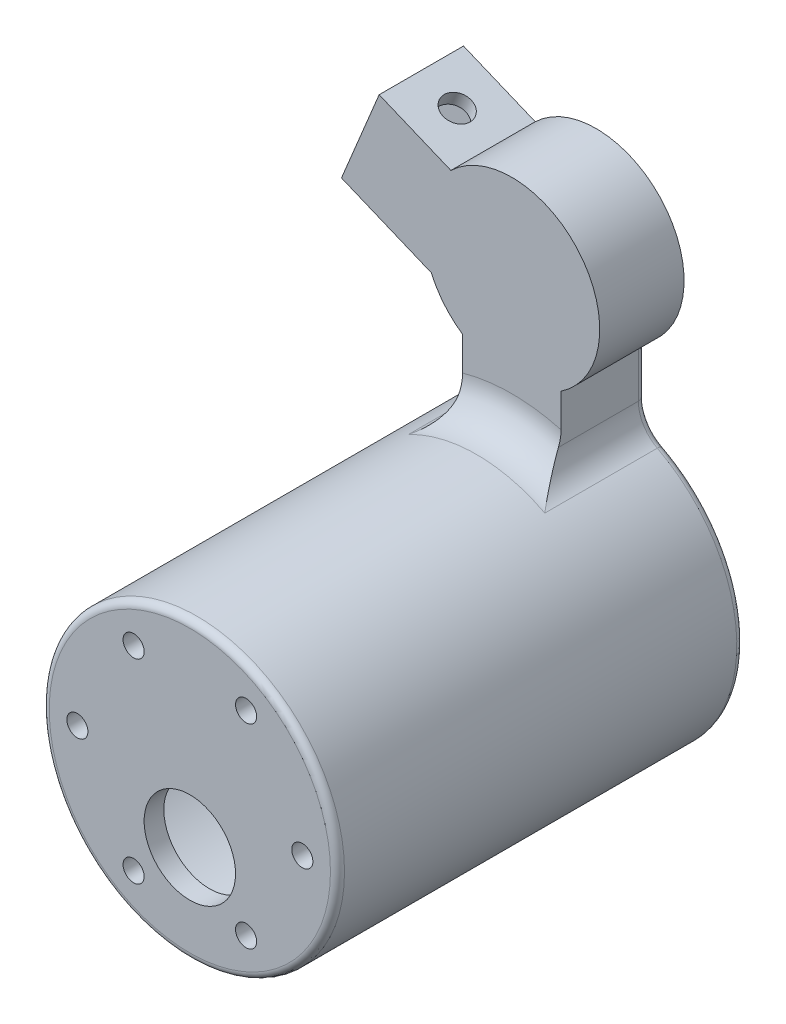
SolidWorks part; units mm, degrees
ref_plane "Front Plane" through (0, 0, 0) normal (0, 0, 1) x (1, 0, 0)
ref_plane "Top Plane" through (0, 0, 0) normal (0, 1, 0) x (1, 0, 0)
ref_plane "Right Plane" through (0, 0, 0) normal (1, 0, 0) x (0, 0, -1)
sketch "Sketch1" plane through (0, 0, 0) normal (0, 0, 1) x (1, 0, 0)
  line L0 (0, 0) -> (-12.5, 0) construction
  line L1 (0, 0) -> (-11.5485, -4.7835) construction
  line L2 (24.2314, 0.2955) -> (11.4585, -4.9953)
  line L3 (0, 0) -> (0, 10) construction
  line L4 (20.7873, 8.6104) -> (24.2314, 0.2955)
  line L5 (20.7873, 8.6104) -> (18.8739, 13.2298)
  line L6 (18.8739, 13.2298) -> (8.671, 9.0036)
  line L8 (0, 0) -> (0, -15.9469) construction
  line L9 (0, -15.9469) -> (-7, -15.9469) construction
  line L12 (-20.7873, -8.6104) -> (-11.5485, -4.7835) construction
  line L15 (0, -15.9469) -> (7, -15.9469) construction
  line L16 (-20.7873, 8.6104) -> (-18.8739, 13.2298)
  line L17 (7, -10.3562) -> (7, -20.3562)
  line L18 (7, -20.3562) -> (-7, -20.3562)
  line L19 (-7, -20.3562) -> (-7, -10.3562)
  line L20 (-18.8739, 13.2298) -> (-8.671, 9.0036)
  line L21 (-20.7873, 8.6104) -> (-24.2314, 0.2955)
  line L22 (-24.2314, 0.2955) -> (-11.4585, -4.9953)
  circle A3 centre (0, 0) radius 12.5
  circle A4 centre (0, 0) radius 10
  dimension "D1" = 25
  dimension "D3" = 22.5
  dimension "D2" = 20
  dimension "D4" = 10
  dimension "D5" = 14
  dimension "D6" = 10
extrude "Boss-Extrude2" add sketch "Sketch1" along normal blind 12 contours A3
sketch "Sketch2" plane through (0, 0, 0) normal (0, 0, 1) x (1, 0, 0)
  line L8 (7, -10.3562) -> (7, -20.3562) construction
  line L9 (7, -20.3562) -> (-7, -20.3562) construction
  line L10 (-7, -20.3562) -> (-7, -10.3562) construction
  line L11 (7, -10.3562) -> (7, -20.3562)
  line L12 (7, -20.3562) -> (-7, -20.3562)
  line L13 (-7, -20.3562) -> (-7, -10.3562)
  line L14 (-24.2314, 0.2955) -> (-11.4585, -4.9953) construction
  line L15 (-20.7873, 8.6104) -> (-24.2314, 0.2955) construction
  line L16 (-20.7873, 8.6104) -> (-18.8739, 13.2298) construction
  line L17 (-18.8739, 13.2298) -> (-8.671, 9.0036) construction
  line L18 (-24.2314, 0.2955) -> (-11.4585, -4.9953)
  line L19 (-20.7873, 8.6104) -> (-24.2314, 0.2955)
  line L20 (-20.7873, 8.6104) -> (-18.8739, 13.2298)
  line L21 (-18.8739, 13.2298) -> (-8.671, 9.0036)
  circle A0 centre (0, 0) radius 12.5 construction
  arc A4 (-8.671, 9.0036) -> (-11.4585, -4.9953) centre (0, 0) ccw
  arc A5 (-7, -10.3562) -> (7, -10.3562) centre (0, 0) ccw
extrude "Boss-Extrude3" add sketch "Sketch2" along normal blind 12
sketch "Sketch5" plane through (0, 0, 0) normal (0, 0, 1) x (1, 0, 0)
  line L0 (0, -20.3562) -> (0, -40.1562) construction
  line L2 (-7, -20.3562) -> (7, -20.3562) construction
  circle A1 centre (0, -40.1562) radius 21.001
  dimension "D1" = 19.8
extrude "Boss-Extrude4" add sketch "Sketch5" along normal blind 57.8
sketch "Sketch6" plane through (0, 0, 0) normal (0, 0, -1) x (-1, 0, 0)
  line L0 (-21.001, -40.1562) -> (0, -40.1562) construction
  arc A2 (-7, -20.3562) -> (7, -20.3562) centre (0, -40.1562) ccw construction
  circle A3 centre (0, -40.1562) radius 19
extrude "Cut-Extrude3" cut sketch "Sketch6" against normal blind 55
sketch "Sketch7" plane through (0, 0, 57.8) normal (0, 0, 1) x (1, 0, 0)
  line L0 (-21.001, -40.1562) -> (21.001, -40.1562) construction
  line L1 (0, -40.1562) -> (0, -47.1562) construction
  line L2 (-19, -40.1562) -> (-16, -40.1562) construction
  circle A2 centre (0, -47.1562) radius 6.5
  circle A3 centre (-16, -40.1562) radius 1.5
  circle A5 centre (-8, -54.0126) radius 1.5
  circle A6 centre (8, -54.0126) radius 1.5
  circle A7 centre (16, -40.1562) radius 1.5
  circle A8 centre (8, -26.2998) radius 1.5
  circle A9 centre (-8, -26.2998) radius 1.5
  point P28 (0, -40.1562)
  dimension "D1" = 7
  dimension "D2" = 6
extrude "Cut-Extrude4" cut sketch "Sketch7" against normal through all
fillet "Fillet1" radius 5 3 edges at (7, -20.3562, 6) (-7, -20.3562, 6) (0, -19.1552, 12)
fillet "Fillet2" radius 1 7 edges at (-7, -13.7231, 0) (7, -13.7231, 0) (-7.7258, -19.6844, 0) (7.7258, -19.6844, 0) (0, -61.1571, 0) (-19, -40.1562, 0) (21.001, -40.1562, 57.8)
sketch "Sketch8" plane through (-20.7873, 8.6104, 0) normal (-0.9239, 0.3827, 0) x (0, 0, 1)
  line L0 (12, 5) -> (0, 5) construction
  line L1 (2, 3) -> (10, 3)
  line L2 (2, 3) -> (2, -7)
  line L3 (2, -7) -> (10, -7)
  line L4 (10, 3) -> (10, -7)
  line L5 (12, -9) -> (0, -9) construction
  line L6 (0, 5) -> (0, -9) construction
  line L7 (12, 5) -> (12, -9) construction
  dimension "D1" = 2
  dimension "D2" = 2
  dimension "D3" = 2
  dimension "D4" = 2
extrude "Cut-Extrude5" cut sketch "Sketch8" against normal blind 10
sketch "Sketch9" plane through (1.9134, 4.6194, 0) normal (0.3827, 0.9239, 0) x (0.9239, -0.3827, 0)
  line L0 (-16.9782, 0) -> (-16.9782, -12) construction
  line L5 (-22.5, -6) -> (-11.4564, -6) construction
  circle A0 centre (-16.9782, -6) radius 2
extrude "Cut-Extrude6" cut sketch "Sketch9" against normal through all
